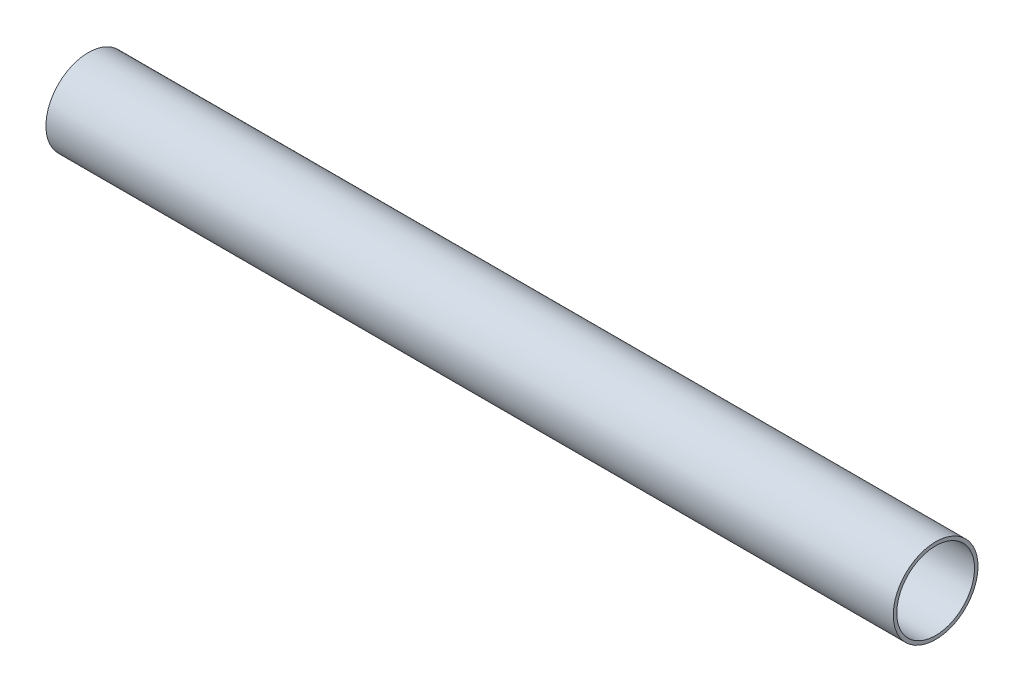
SolidWorks part; units mm, degrees
ref_plane "Front Plane" through (0, 0, 0) normal (0, 0, 1) x (1, 0, 0)
ref_plane "Top Plane" through (0, 0, 0) normal (0, 1, 0) x (1, 0, 0)
ref_plane "Right Plane" through (0, 0, 0) normal (1, 0, 0) x (0, 0, -1)
sketch "Sketch1" plane through (0, 0, 0) normal (1, 0, 0) x (0, 0, -1)
  circle A0 centre (0, 0) radius 14.68
  circle A1 centre (0, 0) radius 16
  dimension "D1" = 29.36
  dimension "D2" = 32
extrude "Boss-Extrude1" add sketch "Sketch1" along normal mid plane 320
